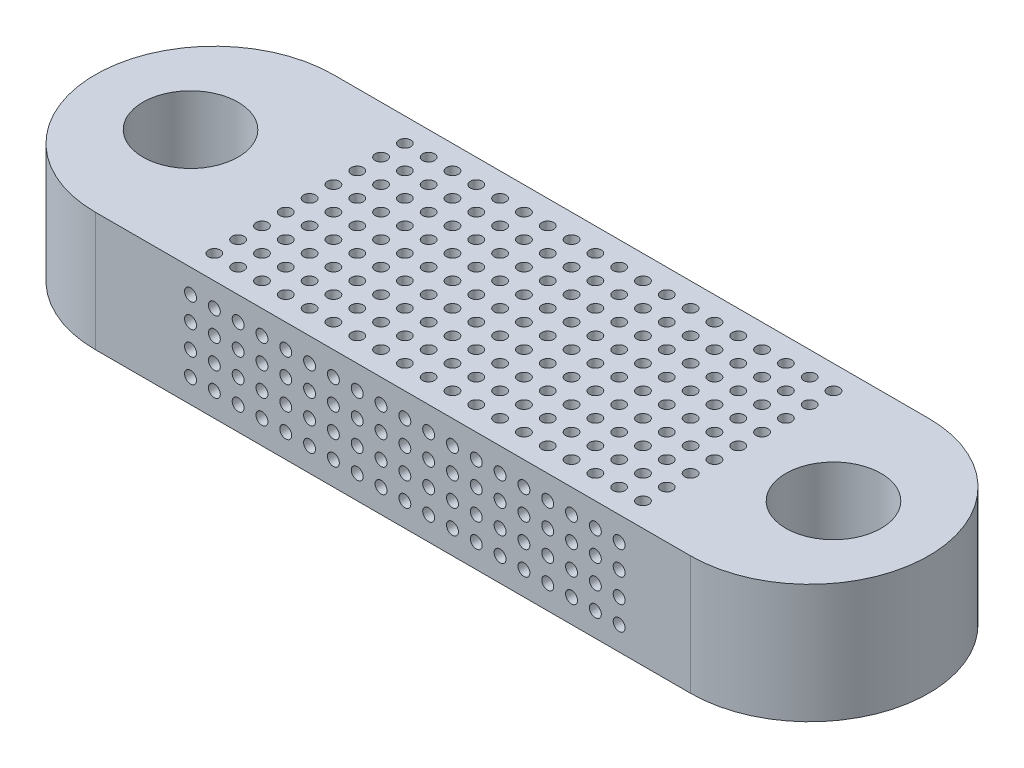
SolidWorks part; units mm, degrees
ref_plane "Front" through (0, 0, 0) normal (0, 0, 1) x (1, 0, 0)
ref_plane "Top" through (0, 0, 0) normal (0, 1, 0) x (1, 0, 0)
ref_plane "Right" through (0, 0, 0) normal (1, 0, 0) x (0, 0, -1)
sketch "Sketch1" plane through (0, 0, 0) normal (0, 1, 0) x (1, 0, 0)
  line L1 (0, 0) -> (50, 0)
  line L2 (0, 0) -> (0, 20)
  line L3 (0, 20) -> (50, 20)
  line L4 (50, 0) -> (50, 20)
extrude "Boss-Extrude1" add sketch "Sketch1" along normal blind 10
sketch "Sketch2" plane through (0, 10, 0) normal (0, 1, 0) x (1, 0, 0)
  circle A0 centre (0, 10) radius 10
extrude "Boss-Extrude2" add sketch "Sketch2" against normal blind 10
sketch "Sketch3" plane through (0, 10, 0) normal (0, 1, 0) x (1, 0, 0)
  circle A0 centre (50, 10) radius 10
extrude "Boss-Extrude3" add sketch "Sketch3" against normal blind 10
sketch "Sketch4" plane through (0, 10, 0) normal (0, 1, 0) x (1, 0, 0)
  circle A0 centre (52, 10) radius 4
  dimension "D1" = 8
extrude "Cut-Extrude1" cut sketch "Sketch4" against normal through all
sketch "Sketch5" plane through (0, 10, 0) normal (0, 1, 0) x (1, 0, 0)
  circle A0 centre (-2, 10) radius 4
extrude "Cut-Extrude2" cut sketch "Sketch5" against normal through all
sketch "Sketch6" plane through (0, 10, 0) normal (0, 1, 0) x (1, 0, 0)
  circle A0 centre (8, 2) radius 0.5
extrude "Cut-Extrude3" cut sketch "Sketch6" against normal through all
sketch "Sketch7" plane through (0, 10, 0) normal (0, 1, 0) x (1, 0, 0)
  circle A0 centre (10, 2) radius 0.5
extrude "Cut-Extrude4" cut sketch "Sketch7" against normal through all
sketch "Sketch8" plane through (0, 10, 0) normal (0, 1, 0) x (1, 0, 0)
  circle A0 centre (12, 2) radius 0.5
extrude "Cut-Extrude5" cut sketch "Sketch8" against normal through all
sketch "Sketch9" plane through (0, 10, 0) normal (0, 1, 0) x (1, 0, 0)
  circle A0 centre (14, 2) radius 0.5
extrude "Cut-Extrude6" cut sketch "Sketch9" against normal through all
sketch "Sketch10" plane through (0, 10, 0) normal (0, 1, 0) x (1, 0, 0)
  circle A0 centre (16, 2) radius 0.5
extrude "Cut-Extrude7" cut sketch "Sketch10" against normal through all
sketch "Sketch11" plane through (0, 10, 0) normal (0, 1, 0) x (1, 0, 0)
  circle A0 centre (18, 2) radius 0.5
extrude "Cut-Extrude8" cut sketch "Sketch11" against normal blind 10
sketch "Sketch12" plane through (0, 10, 0) normal (0, 1, 0) x (1, 0, 0)
  circle A0 centre (20, 2) radius 0.5
extrude "Cut-Extrude9" cut sketch "Sketch12" against normal through all
sketch "Sketch13" plane through (0, 10, 0) normal (0, 1, 0) x (1, 0, 0)
  circle A0 centre (22, 2) radius 0.5
extrude "Cut-Extrude10" cut sketch "Sketch13" against normal through all
sketch "Sketch14" plane through (0, 10, 0) normal (0, 1, 0) x (1, 0, 0)
  circle A0 centre (22, 2) radius 0.5
sketch "Sketch15" plane through (0, 10, 0) normal (0, 1, 0) x (1, 0, 0)
  circle A0 centre (24, 2) radius 0.5
extrude "Cut-Extrude14" cut sketch "Sketch15" against normal through all
pattern_linear "LPattern2" count 1 spacing 2 along (1, 0, 0) count 11 spacing 2 along (1, 0, 0) of "Cut-Extrude14"
sketch "Sketch16" plane through (0, 10, 0) normal (0, 1, 0) x (1, 0, 0)
  circle A0 centre (8, 4) radius 0.5
extrude "Cut-Extrude15" cut sketch "Sketch16" against normal through all
pattern_linear "LPattern3" count 19 spacing 2 along (1, 0, 0) of "Cut-Extrude15"
sketch "Sketch17" plane through (0, 10, 0) normal (0, 1, 0) x (1, 0, 0)
  circle A0 centre (8, 6) radius 0.5
extrude "Cut-Extrude16" cut sketch "Sketch17" against normal through all
pattern_linear "LPattern4" count 19 spacing 2 along (1, 0, 0) of "Cut-Extrude16"
sketch "Sketch18" plane through (0, 10, 0) normal (0, 1, 0) x (1, 0, 0)
  circle A0 centre (8, 8) radius 0.5
extrude "Cut-Extrude17" cut sketch "Sketch18" against normal through all
sketch "Sketch19" plane through (0, 10, 0) normal (0, 1, 0) x (1, 0, 0)
  circle A0 centre (8, 10) radius 0.5
extrude "Cut-Extrude18" cut sketch "Sketch19" against normal through all
sketch "Sketch20" plane through (0, 10, 0) normal (0, 1, 0) x (1, 0, 0)
  circle A0 centre (8, 12) radius 0.5
extrude "Cut-Extrude19" cut sketch "Sketch20" against normal through all
pattern_linear "LPattern5" count 19 spacing 2 along (1, 0, 0) of "Cut-Extrude17"
pattern_linear "LPattern6" count 19 spacing 2 along (1, 0, 0) of "Cut-Extrude18"
pattern_linear "LPattern7" count 19 spacing 2 along (1, 0, 0) of "Cut-Extrude19"
sketch "Sketch21" plane through (0, 10, 0) normal (0, 1, 0) x (1, 0, 0)
  circle A0 centre (8, 14) radius 0.5
extrude "Cut-Extrude20" cut sketch "Sketch21" against normal through all
sketch "Sketch22" plane through (0, 10, 0) normal (0, 1, 0) x (1, 0, 0)
  circle A0 centre (8, 16) radius 0.5
extrude "Cut-Extrude21" cut sketch "Sketch22" against normal through all
sketch "Sketch23" plane through (0, 10, 0) normal (0, 1, 0) x (1, 0, 0)
  circle A0 centre (8, 18) radius 0.5
extrude "Cut-Extrude22" cut sketch "Sketch23" against normal through all
pattern_linear "LPattern8" count 19 spacing 2 along (1, 0, 0) of "Cut-Extrude20"
pattern_linear "LPattern9" count 19 spacing 2 along (1, 0, 0) of "Cut-Extrude21"
pattern_linear "LPattern10" count 19 spacing 2 along (1, 0, 0) of "Cut-Extrude22"
sketch "Sketch25" plane through (0, 0, 0) normal (0, 0, 1) x (1, 0, 0)
  circle A0 centre (8, 8) radius 0.5
extrude "Cut-Extrude24" cut sketch "Sketch25" against normal through all
pattern_linear "LPattern13" count 4 spacing 2 along (0, -1, 0) count 19 spacing 2 along (1, 0, 0) of "Cut-Extrude24"
